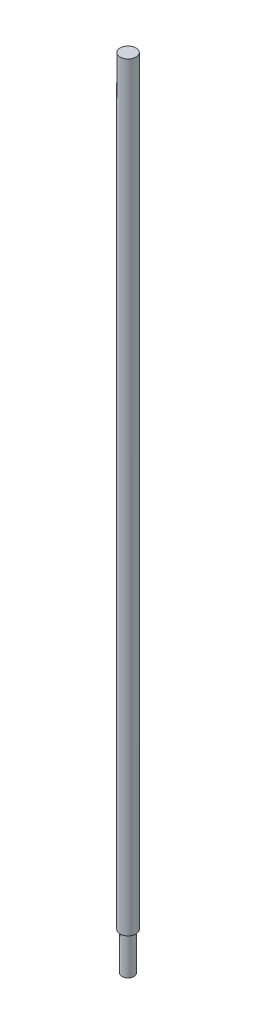
SolidWorks part; units mm, degrees
ref_plane "Ebene vorne" through (0, 0, 0) normal (0, 0, 1) x (1, 0, 0)
ref_plane "Ebene oben" through (0, 0, 0) normal (0, 1, 0) x (1, 0, 0)
ref_plane "Ebene rechts" through (0, 0, 0) normal (1, 0, 0) x (0, 0, -1)
sketch "Position" plane through (0, 0, 0) normal (0, 1, 0) x (1, 0, 0)
  circle A0 centre (14, 0) radius 1.5
  circle A1 centre (0, 0) radius 4.5
sketch "Length" plane through (0, 0, 0) normal (0, 0, 1) x (1, 0, 0)
  line L0 (0, 218) -> (0, 618)
  line L4 (14, 237) -> (14, 618)
sketch "Skizze3" plane through (0, 0, 0) normal (0, 1, 0) x (1, 0, 0)
  line L0 (-23.35, 0) -> (23.35, 0) construction
  circle A0 centre (0, 0) radius 4
extrude "Aufsatz-Linear austragen1" add sketch "Skizze3" along normal up to vertex (618 mm away) from vertex at 218 starting at point (0, 218, 0)
sketch "Skizze5" plane through (0, 218, 0) normal (0, -1, 0) x (1, 0, 0)
  circle A0 centre (0, 0) radius 4
  circle A1 centre (0, 0) radius 3
extrude "Schnitt-Linear austragen1" cut sketch "Skizze5" against normal up to vertex (19 mm away) up to point (14, 237, 0)
